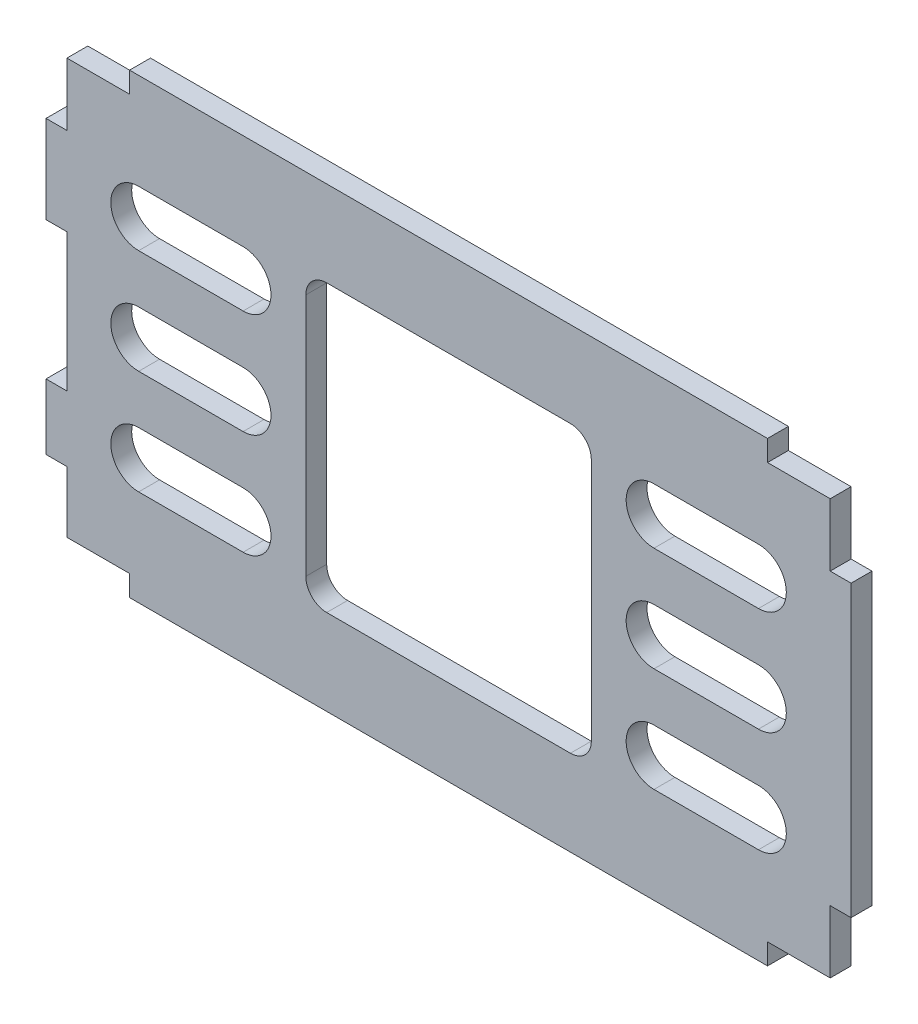
SolidWorks part; units mm, degrees
material "ABS PC"
ref_plane "정면" through (0, 0, 0) normal (0, 0, 1) x (1, 0, 0)
ref_plane "윗면" through (0, 0, 0) normal (0, 1, 0) x (1, 0, 0)
ref_plane "우측면" through (0, 0, 0) normal (1, 0, 0) x (0, 0, -1)
ref_plane "평면2" through (0, 0, 70) normal (0, 0, 1) x (1, 0, 0)
sketch "스케치5" plane through (0, 0, 70) normal (0, 0, 1) x (1, 0, 0)
  line L0 (54.8, -20.8) -> (57.8, -20.8)
  line L1 (57.8, -20.8) -> (57.8, 20.8)
  line L2 (57.8, 20.8) -> (54.8, 20.8)
  line L3 (54.8, 20.8) -> (54.8, 29.8)
  line L4 (54.8, 29.8) -> (45.8, 29.8)
  line L5 (45.8, 29.8) -> (45.8, 32.8)
  line L6 (45.8, 32.8) -> (-45.8, 32.8)
  line L7 (-45.8, 32.8) -> (-45.8, 29.8)
  line L8 (-45.8, 29.8) -> (-54.8, 29.8)
  line L9 (-54.8, 29.8) -> (-54.8, 20.8)
  line L10 (-54.8, 20.8) -> (-57.8, 20.8)
  line L11 (-57.8, 20.8) -> (-57.8, 8.2)
  line L12 (-57.8, 8.2) -> (-54.8, 8.2)
  line L13 (-54.8, 8.2) -> (-54.8, -11.6)
  line L14 (-54.8, -11.6) -> (-57.8, -11.6)
  line L15 (-57.8, -11.6) -> (-57.8, -21)
  line L16 (-57.8, -21) -> (-54.8, -21)
  line L17 (-54.8, -21) -> (-54.8, -29.8)
  line L18 (-54.8, -29.8) -> (-45.8, -29.8)
  line L19 (-45.8, -29.8) -> (-45.8, -32.8)
  line L20 (-45.8, -32.8) -> (45.8, -32.8)
  line L21 (45.8, -32.8) -> (45.8, -29.8)
  line L22 (45.8, -29.8) -> (54.8, -29.8)
  line L23 (54.8, -29.8) -> (54.8, -20.8)
  line L24 (-17.5, 20.5) -> (17.5, 20.5)
  line L25 (20.5, 17.5) -> (20.5, -17.5)
  line L26 (17.5, -20.5) -> (-17.5, -20.5)
  line L27 (-20.5, -17.5) -> (-20.5, 17.5)
  line L28 (-29.5, 11) -> (-44.5, 11)
  line L29 (-44.5, 19) -> (-29.5, 19)
  line L30 (29.5, -11) -> (44.5, -11)
  line L31 (44.5, -19) -> (29.5, -19)
  line L32 (29.5, 4) -> (44.5, 4)
  line L33 (44.5, -4) -> (29.5, -4)
  line L34 (29.5, 19) -> (44.5, 19)
  line L35 (44.5, 11) -> (29.5, 11)
  line L36 (-29.5, -19) -> (-44.5, -19)
  line L37 (-44.5, -11) -> (-29.5, -11)
  line L38 (-29.5, -4) -> (-44.5, -4)
  line L39 (-44.5, 4) -> (-29.5, 4)
  arc A0 (17.5, 20.5) -> (20.5, 17.5) centre (17.5, 17.5) cw
  arc A1 (20.5, -17.5) -> (17.5, -20.5) centre (17.5, -17.5) cw
  arc A2 (-17.5, -20.5) -> (-20.5, -17.5) centre (-17.5, -17.5) cw
  arc A3 (-20.5, 17.5) -> (-17.5, 20.5) centre (-17.5, 17.5) cw
  arc A4 (-29.5, 19) -> (-29.5, 11) centre (-29.5, 15) cw
  arc A5 (-44.5, 11) -> (-44.5, 19) centre (-44.5, 15) cw
  arc A6 (44.5, -11) -> (44.5, -19) centre (44.5, -15) cw
  arc A7 (29.5, -19) -> (29.5, -11) centre (29.5, -15) cw
  arc A8 (44.5, 4) -> (44.5, -4) centre (44.5, 0) cw
  arc A9 (29.5, -4) -> (29.5, 4) centre (29.5, 0) cw
  arc A10 (44.5, 19) -> (44.5, 11) centre (44.5, 15) cw
  arc A11 (29.5, 11) -> (29.5, 19) centre (29.5, 15) cw
  arc A12 (-29.5, -11) -> (-29.5, -19) centre (-29.5, -15) cw
  arc A13 (-44.5, -19) -> (-44.5, -11) centre (-44.5, -15) cw
  arc A14 (-29.5, 4) -> (-29.5, -4) centre (-29.5, 0) cw
  arc A15 (-44.5, -4) -> (-44.5, 4) centre (-44.5, 0) cw
extrude "보스-돌출2" add sketch "스케치5" against normal blind 3 separate body
